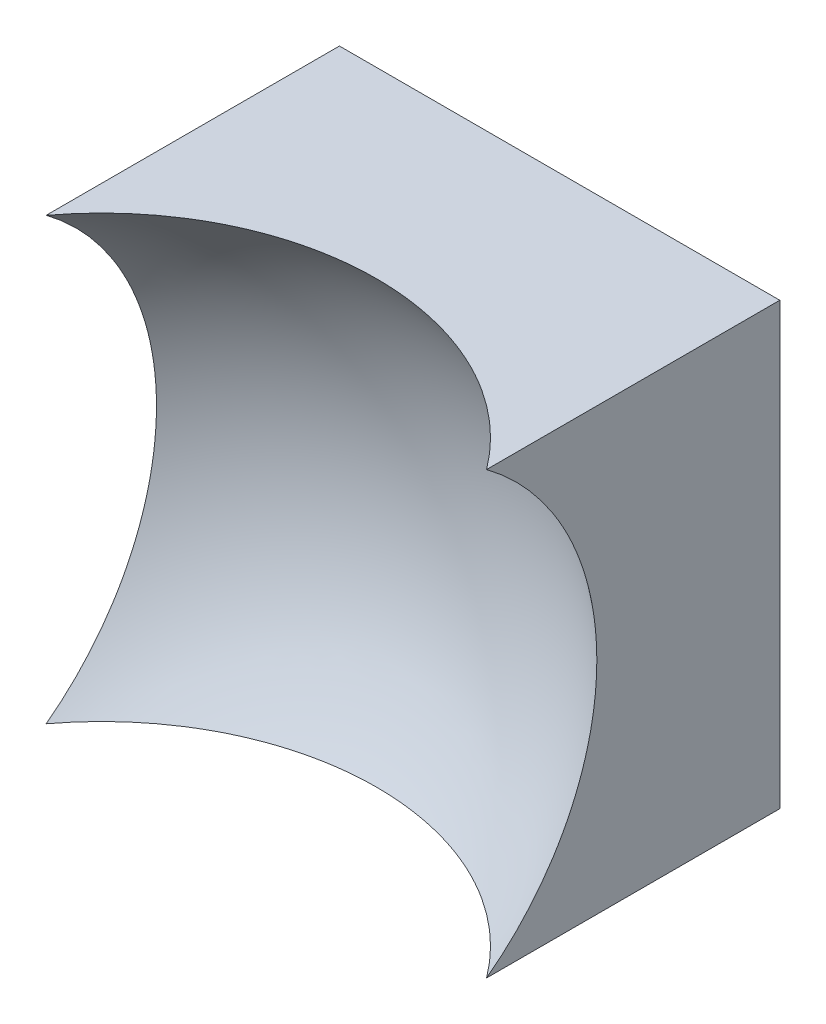
SolidWorks part; units mm, degrees
ref_plane "前视基准面" through (0, 0, 0) normal (0, 0, 1) x (1, 0, 0)
ref_plane "上视基准面" through (0, 0, 0) normal (0, 1, 0) x (1, 0, 0)
ref_plane "右视基准面" through (0, 0, 0) normal (1, 0, 0) x (0, 0, -1)
sketch "草图1" plane through (0, 0, 0) normal (0, 0, 1) x (1, 0, 0)
  line L1 (-6.25, 6.25) -> (6.25, 6.25)
  line L2 (-6.25, 6.25) -> (-6.25, -6.25)
  line L3 (-6.25, -6.25) -> (6.25, -6.25)
  line L4 (6.25, 6.25) -> (6.25, -6.25)
  line L5 (-6.25, 6.25) -> (6.25, -6.25) construction
  line L6 (-6.25, -6.25) -> (6.25, 6.25) construction
  point P0 (0, 0)
  dimension "D1" = 12.5
  dimension "D2" = 12.5
extrude "凸台-拉伸1" add sketch "草图1" along normal blind 10 contours L2 L3 L4 L1
sketch "草图2" plane through (0, 0, 0) normal (0, 1, 0) x (1, 0, 0)
  line L0 (-7.4603, -3) -> (7.3192, -3) construction
  line L1 (0, 0) -> (0, -12.1749) construction
  line L2 (9.7485, -10.7712) -> (0, -10.7712)
  line L3 (0, -10.7712) -> (0, -3)
  arc A1 (9.7485, -10.7712) -> (0, -3) centre (0, -13) ccw
  dimension "D2" = 20
  dimension "D1" = 3
revolve "切除-旋转2" cut sketch "草图2" angle 360 about L3
